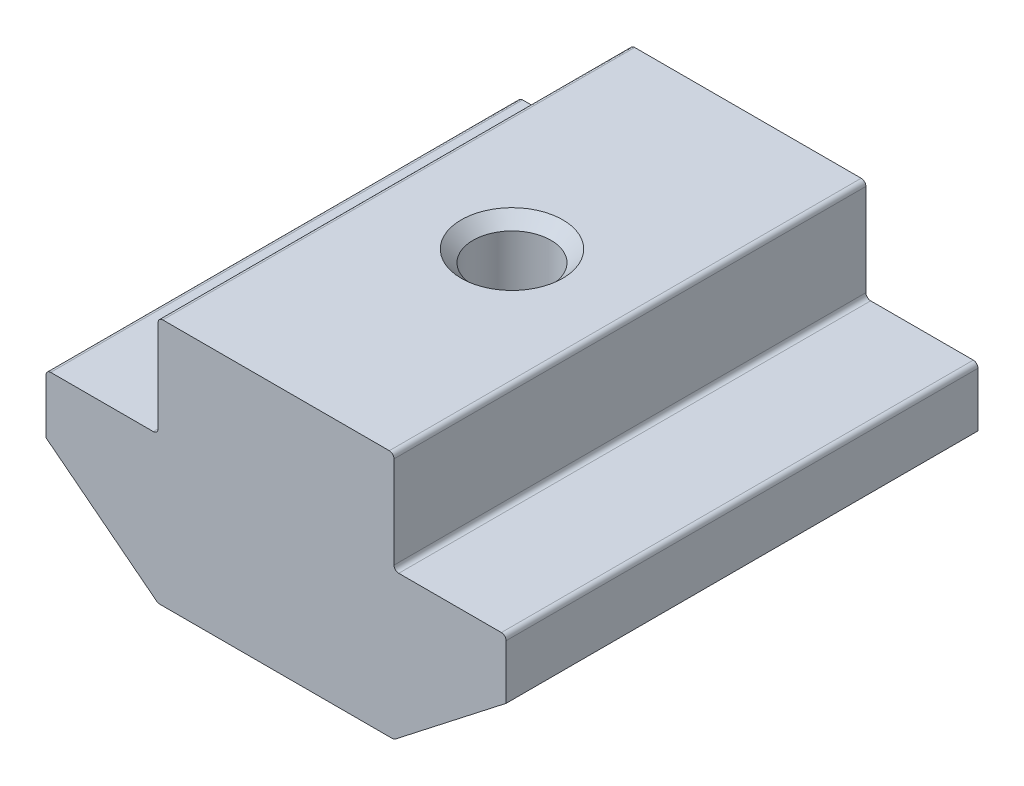
SolidWorks part; units mm, degrees
ref_plane "Спереди" through (0, 0, 0) normal (0, 0, 1) x (1, 0, 0)
ref_plane "Сверху" through (0, 0, 0) normal (0, 1, 0) x (1, 0, 0)
ref_plane "Справа" through (0, 0, 0) normal (1, 0, 0) x (0, 0, -1)
sketch "Эскиз1" plane through (0, 0, 0) normal (0, 0, 1) x (1, 0, 0)
  line L0 (5, 0) -> (-5, 0)
  line L1 (-5, 0) -> (-5, -4.3)
  line L2 (-5, -4.3) -> (-9.75, -4.3)
  line L3 (-9.75, -4.3) -> (-9.75, -6.8)
  line L4 (-9.75, -6.8) -> (-5, -10.5)
  line L5 (-5, -10.5) -> (5, -10.5)
  line L6 (0, -10.5) -> (0, 0) construction
  line L7 (9.75, -6.8) -> (5, -10.5)
  line L8 (9.75, -4.3) -> (9.75, -6.8)
  line L9 (5, -4.3) -> (9.75, -4.3)
  line L10 (5, 0) -> (5, -4.3)
  point P3 (-5, -2.15)
  dimension "D1" = 10
  dimension "D2" = 19.5
  dimension "D3" = 2.5
  dimension "D4" = 10.5
  dimension "D5" = 6.2
extrude "Бобышка-Вытянуть1" add sketch "Эскиз1" along normal mid plane 20
hole_wizard "Отверстие обработанное метчиком M44" positions "Эскиз2" profile "Эскиз4" tap size "M4" standard "ISO" end condition through all
sketch "Эскиз2" plane through (0, 0, 0) normal (0, 1, 0) x (1, 0, 0)
  point P0 (0, 0)
sketch "Эскиз4" plane through (0, 0, 0) normal (1, 0, 0) x (0, 0, 1)
  line L0 (0, 0) -> (0, 10.5)
  line L1 (0, 10.5) -> (2.15, 10.5)
  line L2 (1.65, 10) -> (1.65, 0.5)
  line L3 (1.65, 0.5) -> (2.15, 0)
  line L5 (2.15, 0) -> (0, 0)
  line L6 (-1.65, 0.5) -> (-2.15, 0) construction
  line L7 (2.15, 10.5) -> (1.65, 10)
  line L8 (-2.15, 10.5) -> (-1.65, 10) construction
  line L11 (0, -6.35) -> (0, 107.95) construction
  dimension "Диаметр проходного сверла" = 3.3
  dimension "Глубина проходного сверла" = 10.5
  dimension "Диаметр передней зенковки" = 4.3
  dimension "Угол передней зенковки" = 90
  dimension "Диаметр задней зенковки" = 4.3
  dimension "Угол задней зенковки" = 90
cosmetic thread "Отверстие резьбы1" parameters "D2"=4
fillet "Скругление1" radius 0.2 8 edges at (5, -10.5, 0) (-5, -10.5, 0) (9.75, -4.3, 0) (5, -4.3, 0) (5, 0, 0) (-5, 0, 0) (-9.75, -4.3, 0) (-5, -4.3, 0)
